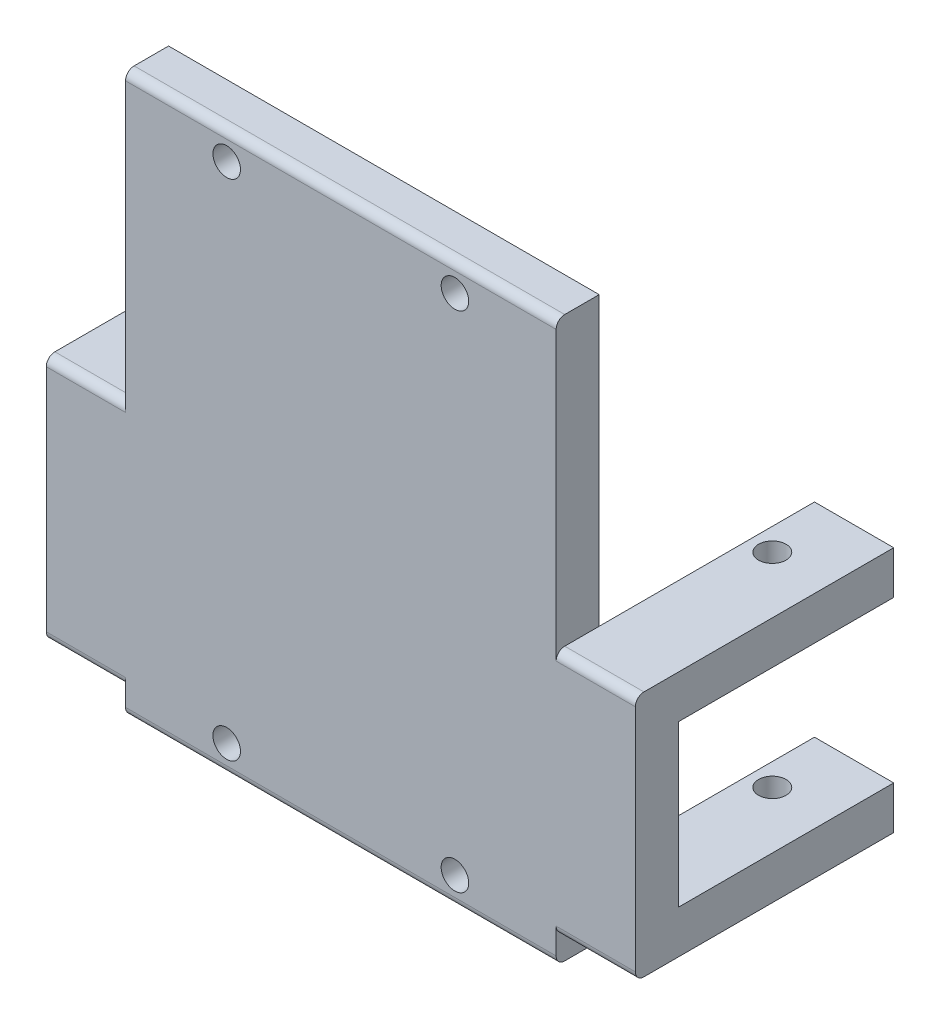
SolidWorks part; units mm, degrees
ref_plane "Front Plane" through (0, 0, 0) normal (0, 0, 1) x (1, 0, 0)
ref_plane "Top Plane" through (0, 0, 0) normal (0, 1, 0) x (1, 0, 0)
ref_plane "Right Plane" through (0, 0, 0) normal (1, 0, 0) x (0, 0, -1)
sketch "Sketch1" plane through (0, 0, 0) normal (0, 0, 1) x (1, 0, 0)
  line L0 (0, 32.5) -> (0, -32.5) construction
  line L1 (-25, 32.5) -> (25, 32.5)
  line L2 (-25, 32.5) -> (-25, -32.5)
  line L3 (-25, -32.5) -> (25, -32.5)
  line L4 (25, 32.5) -> (25, -32.5)
  line L5 (-25, 32.5) -> (25, -32.5) construction
  line L6 (-25, -32.5) -> (25, 32.5) construction
  line L7 (-27.6, 0) -> (27.6, 0) construction
  line L8 (0, 14.325) -> (0, -14.325)
  line L10 (-29.2, 19.325) -> (-26, 19.325)
  line L11 (-29.2, 19.325) -> (-29.2, 14.325)
  line L12 (-29.2, 14.325) -> (-26, 14.325)
  line L13 (-26, 19.325) -> (-26, 14.325)
  line L14 (-29.2, 19.325) -> (-26, 14.325) construction
  line L15 (-29.2, 14.325) -> (-26, 19.325) construction
  circle A0 centre (-13.25, 29.25) radius 1.6
  circle A1 centre (13.25, 29.25) radius 1.6
  circle A2 centre (13.25, -29.25) radius 1.6
  circle A3 centre (-13.25, -29.25) radius 1.6
  point P0 (0, 0)
  point P20 (-27.6, 16.825)
  dimension "D3" = 3.2
  dimension "D1" = 50
  dimension "D2" = 65
  dimension "D4" = 13.25
  dimension "D5" = 29.25
  dimension "D6" = 28.65
  dimension "D7" = 55.2
  dimension "D8" = 3.2
  dimension "D9" = 5
sketch "Sketch2" plane through (0, 0, 0) normal (0, 0, 1) x (1, 0, 0)
  line L0 (25, 32.5) -> (25, -32.5) construction
  line L1 (-25, -32.5) -> (25, -32.5) construction
  line L2 (-25, 32.5) -> (-25, -32.5) construction
  line L3 (-25, 32.5) -> (25, 32.5) construction
  line L4 (25, 32.5) -> (25, -32.5)
  line L5 (-25, -32.5) -> (25, -32.5)
  line L6 (-25, 32.5) -> (-25, -32.5)
  line L7 (-25, 32.5) -> (25, 32.5)
  line L8 (0, 32.5) -> (0, -32.5) construction
  line L9 (-45, 10) -> (-25, 10)
  line L10 (-45, 10) -> (-45, -10)
  line L11 (-45, -10) -> (-25, -10)
  line L12 (-25, 10) -> (-25, -10)
  line L13 (-45, 10) -> (-25, -10) construction
  line L14 (-45, -10) -> (-25, 10) construction
  line L15 (0, 32.5) -> (0, -32.5) construction
  line L16 (45, 10) -> (45, -10)
  line L17 (45, -10) -> (25, -10)
  line L18 (25, 10) -> (25, -10)
  line L19 (45, 10) -> (25, 10)
  line L20 (-29.2, 19.325) -> (-29.2, 14.325) construction
  line L21 (34.2, -24.5) -> (-34.2, -24.5)
  line L22 (34.2, -24.5) -> (34.2, -29.5)
  line L23 (34.2, -29.5) -> (-34.2, -29.5)
  line L24 (-34.2, -24.5) -> (-34.2, -29.5)
  line L25 (34.2, -24.5) -> (-34.2, -29.5) construction
  line L26 (34.2, -29.5) -> (-34.2, -24.5) construction
  circle A0 centre (-13.25, 29.25) radius 1.6 construction
  circle A1 centre (13.25, 29.25) radius 1.6 construction
  circle A2 centre (13.25, -29.25) radius 1.6 construction
  circle A3 centre (-13.25, -29.25) radius 1.6 construction
  circle A4 centre (-13.25, 29.25) radius 1.6
  circle A5 centre (13.25, 29.25) radius 1.6
  circle A6 centre (13.25, -29.25) radius 1.6
  circle A7 centre (-13.25, -29.25) radius 1.6
  circle A8 centre (-35, 0) radius 1.6
  circle A9 centre (35, 0) radius 1.6
  point P16 (-35, 0)
  point P32 (0, -27)
  dimension "D1" = 3.2
  dimension "D2" = 10
  dimension "D3" = 20
  dimension "D4" = 5
  dimension "D5" = 3
  dimension "D6" = 5
extrude "Boss-Extrude1" add sketch "Sketch2" along normal blind 5 contours L7 L6 L5 L4 A7 A6 A5 A4 | L23 L22 L21 L4 | L23 L4 L21 L6 A7 A6 | L21 L24 L23 L6 | A7 L23 L6 L5 L4 A6
sketch "Sketch3" plane through (0, 0, 0) normal (0, 0, -1) x (-1, 0, 0)
  line L0 (-53.1397, -0.85) -> (59.2981, -0.85) construction
  line L1 (-52.4413, -29.5) -> (59.2981, -29.5) construction
  line L3 (0, 14.325) -> (0, -14.325) construction
  line L4 (-34.2, -24.5) -> (-25, -24.5)
  line L5 (-34.2, -24.5) -> (-34.2, -29.5)
  line L6 (-34.2, -29.5) -> (-25, -29.5)
  line L7 (-25, -24.5) -> (-25, -29.5)
  line L8 (-34.2, -0.85) -> (-25, -0.85)
  line L9 (-34.2, -0.85) -> (-34.2, -5.85)
  line L10 (-34.2, -5.85) -> (-25, -5.85)
  line L11 (-25, -0.85) -> (-25, -5.85)
  line L12 (0, 14.325) -> (0, -14.325)
  line L13 (34.2, -24.5) -> (34.2, -29.5)
  line L14 (34.2, -29.5) -> (25, -29.5)
  line L15 (25, -24.5) -> (25, -29.5)
  line L16 (34.2, -24.5) -> (25, -24.5)
  line L17 (34.2, -0.85) -> (34.2, -5.85)
  line L18 (34.2, -5.85) -> (25, -5.85)
  line L19 (25, -0.85) -> (25, -5.85)
  line L20 (34.2, -0.85) -> (25, -0.85)
  line L21 (-34.2, -29.5) -> (-25, -29.5) construction
  dimension "D1" = 28.65
  dimension "D2" = 5
extrude "Boss-Extrude2" add sketch "Sketch3" along normal blind 25 and the other way up to surface (5 mm away)
sketch "Sketch4" plane through (0, -0.85, 0) normal (0, 1, 0) x (1, 0, 0)
  line L2 (34.2, 25) -> (25, 25) construction
  line L3 (0, 0) -> (0, 19.5448) construction
  line L4 (-27.6, 0) -> (-27.6, 17.5) construction
  circle A0 centre (27.6, 17.5) radius 1.6
  circle A1 centre (-27.6, 17.5) radius 1.6
  point P0 (27.6, 17.5)
  dimension "D1" = 3.2
  dimension "D2" = 7.5
extrude "Cut-Extrude1" cut sketch "Sketch4" against normal through all
sketch "Sketch5" plane through (0, 0, 5) normal (0, 0, 1) x (1, 0, 0)
  line L1 (-34.2, -5.85) -> (-25, -5.85)
  line L2 (-34.2, -5.85) -> (-34.2, -24.5)
  line L3 (-34.2, -24.5) -> (-25, -24.5)
  line L4 (-25, -5.85) -> (-25, -24.5)
  line L5 (25, -5.85) -> (34.2, -5.85)
  line L6 (25, -5.85) -> (25, -24.5)
  line L7 (25, -24.5) -> (34.2, -24.5)
  line L8 (34.2, -5.85) -> (34.2, -24.5)
extrude "Boss-Extrude3" add sketch "Sketch5" against normal up to surface (5 mm away) up to face at (-11.65, 29.25, 0)
fillet "Fillet1" radius 1 6 edges at (-29.6, -29.5, 5) (0, -32.5, 5) (29.6, -29.5, 5) (0, 32.5, 5) (-29.6, -0.85, 5) (29.6, -0.85, 5)
